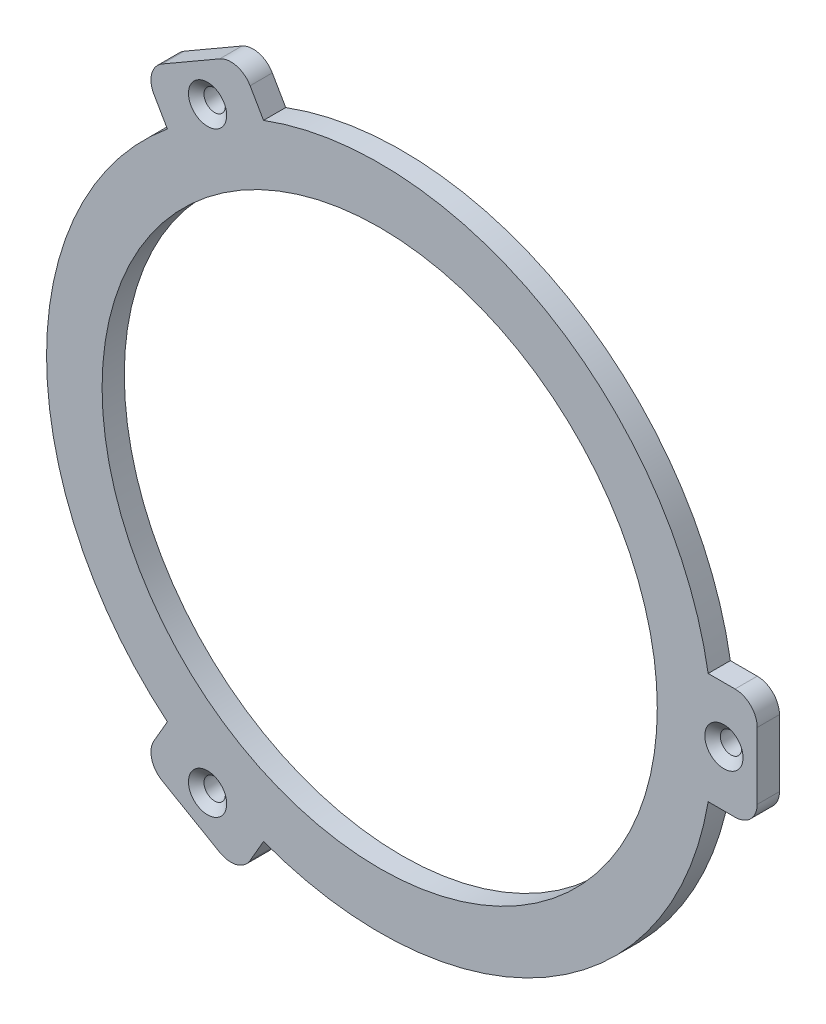
SolidWorks part; units mm, degrees
other "DetailItem1"
ref_plane "Front Plane" through (0, 0, 0) normal (0, 0, 1) x (1, 0, 0)
ref_plane "Top Plane" through (0, 0, 0) normal (0, 1, 0) x (1, 0, 0)
ref_plane "Right Plane" through (0, 0, 0) normal (1, 0, 0) x (0, 0, -1)
sketch "Sketch1" plane through (0, 0, 0) normal (0, 0, 1) x (1, 0, 0)
  circle A0 centre (0, 0) radius 31.75
  circle A1 centre (0, 0) radius 38.1
  dimension "D2" = 76.2
  dimension "D1" = 6.35
extrude "Boss-Extrude1" add sketch "Sketch1" along normal blind 2.54
sketch "Sketch2" plane through (0, 0, 0) normal (0, 0, 1) x (1, 0, 0)
  line L1 (43.18, 6.35) -> (33.02, 6.35)
  line L2 (43.18, 6.35) -> (43.18, -6.35)
  line L3 (43.18, -6.35) -> (33.02, -6.35)
  line L4 (33.02, 6.35) -> (33.02, -6.35)
  dimension "D1" = 12.7
  dimension "D2" = 6.35
  dimension "D3" = 43.18
  dimension "D4" = 10.16
extrude "Boss-Extrude2" add sketch "Sketch2" along normal blind 2.54
fillet "Fillet1" radius 2.54 2 edges at (43.18, -6.35, 1.27) (43.18, 6.35, 1.27)
sketch "Sketch3" plane through (0, 0, 2.54) normal (0, 0, 1) x (1, 0, 0)
  circle A0 centre (39.37, 0) radius 0.635
  dimension "D2" = 1.27
  dimension "D1" = 39.37
extrude "Cut-Extrude1" cut sketch "Sketch3" against normal through all
hole_wizard "CSK for #2 Flat Head Machine Screw (100)1" positions "Sketch5" profile "Sketch4" countersink size "#2" standard "ANSI Inch" end condition through all
sketch "Sketch5" plane through (0, 0, 2.54) normal (0, 0, 1) x (1, 0, 0)
  point P0 (39.37, 0)
sketch "Sketch4" plane through (39.37, 0, 2.54) normal (1, 0, 0) x (0, -1, 0)
  line L0 (0, 0) -> (0, 2.54)
  line L1 (0, 2.54) -> (1.2192, 2.54)
  line L2 (1.2192, 2.54) -> (1.2192, 0.8099)
  line L3 (1.2192, 0.8099) -> (2.1844, 0)
  line L5 (2.1844, 0) -> (0, 0)
  line L6 (-1.2192, 0.8099) -> (-2.1844, 0) construction
  line L11 (0, -6.35) -> (0, 107.95) construction
  dimension "Thru Hole Dia." = 2.4384
  dimension "Thru Hole Depth" = 2.54
  dimension "Near C'Sink Dia." = 4.3688
  dimension "Near C'Sink Angle" = 100
pattern_circular "CirPattern1" count 3 over 360 about axis through (0, 0, 0) along (0, 0, 1) of "Boss-Extrude2", "Fillet1", "Cut-Extrude1", "CSK for #2 Flat Head Machine Screw (100)1"
sketch "Sketch6" plane through (0, 0, 0) normal (0, 0, -1) x (-1, 0, 0)
  circle A0 centre (0, 0) radius 34.544
  circle A1 centre (0, 0) radius 36.9697
  dimension "D2" = 73.9394
  dimension "D1" = 69.088
extrude "Cut-Extrude3" cut sketch "Sketch6" against normal blind 1.27
equation "\"D2@Sketch2\"=\"D1@Sketch2\"/2"
